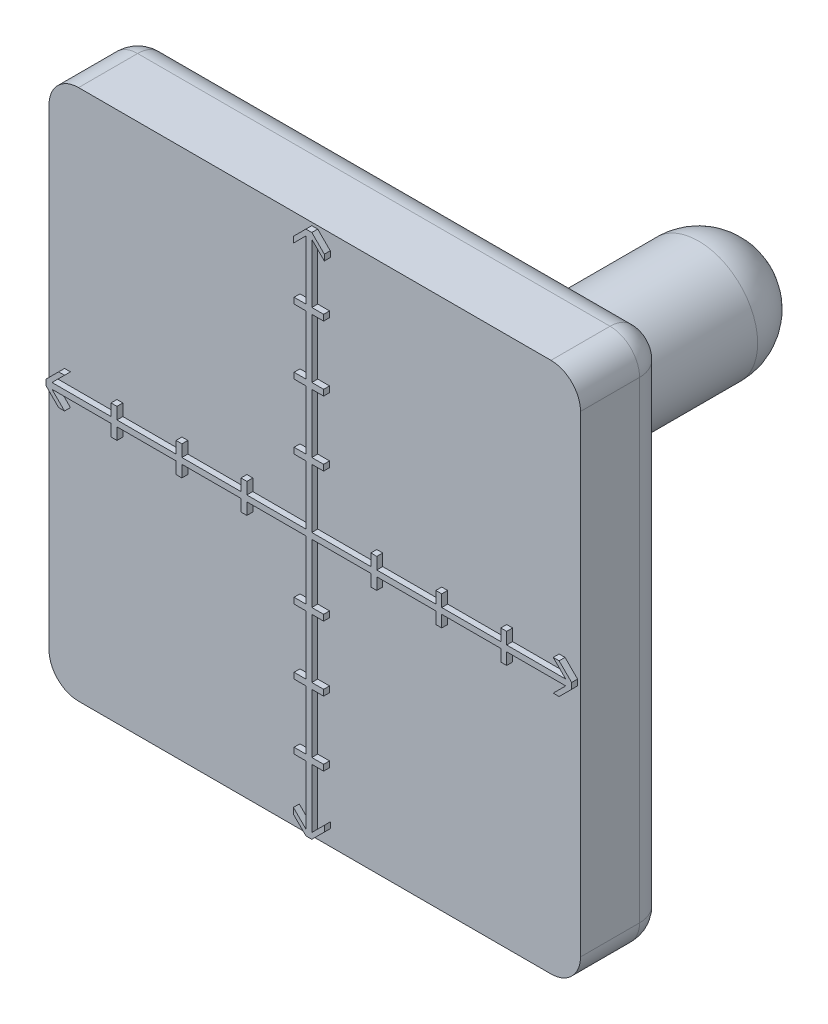
SolidWorks part; units mm, degrees
ref_plane "Alzado" through (0, 0, 0) normal (0, 0, 1) x (1, 0, 0)
ref_plane "Planta" through (0, 0, 0) normal (0, 1, 0) x (1, 0, 0)
ref_plane "Vista lateral" through (0, 0, 0) normal (1, 0, 0) x (0, 0, -1)
sketch "Croquis1" plane through (0, 0, 0) normal (0, 0, 1) x (1, 0, 0)
  line L1 (-45, -45) -> (45, -45)
  line L2 (-45, -45) -> (-45, 45)
  line L3 (-45, 45) -> (45, 45)
  line L4 (45, -45) -> (45, 45)
  line L5 (-45, -45) -> (45, 45) construction
  line L6 (-45, 45) -> (45, -45) construction
  point P0 (0, 0)
  dimension "D1" = 90
  dimension "D2" = 90
extrude "Saliente-Extruir2" add sketch "Croquis1" along normal blind 15
sketch "Croquis2" plane through (0, 0, 0) normal (0, 0, -1) x (-1, 0, 0)
  circle A0 centre (0, 0) radius 10
extrude "Saliente-Extruir3" add sketch "Croquis2" along normal blind 60
sketch "Croquis3" plane through (0, 0, 15) normal (0, 0, 1) x (1, 0, 0)
  line L14 (10.5, 0.5) -> (10.5, 2.5)
  line L15 (10.5, 2.5) -> (11.5, 2.5)
  line L16 (11.5, 2.5) -> (11.5, 0.5)
  line L18 (21.5, 0.5) -> (21.5, 2.5)
  line L19 (21.5, 2.5) -> (22.5, 2.5)
  line L20 (22.5, 2.5) -> (22.5, 0.5)
  line L22 (32.5, 0.5) -> (32.5, 2.5)
  line L23 (32.5, 2.5) -> (33.5, 2.5)
  line L24 (33.5, 2.5) -> (33.5, 0.5)
  line L25 (43.5, 0.5) -> (41.3787, 2.6213)
  line L26 (41.3787, 2.6213) -> (42.3787, 2.6213)
  line L27 (42.3787, 2.6213) -> (44.5, 0.5)
  line L28 (0, -41.25) -> (0, 41.25) construction
  line L29 (-42.3787, 2.6213) -> (-44.5, 0.5)
  line L30 (-41.3787, 2.6213) -> (-42.3787, 2.6213)
  line L31 (-43.5, 0.5) -> (-41.3787, 2.6213)
  line L32 (-33.5, 2.5) -> (-33.5, 0.5)
  line L33 (-32.5, 2.5) -> (-33.5, 2.5)
  line L34 (-32.5, 0.5) -> (-32.5, 2.5)
  line L35 (-22.5, 2.5) -> (-22.5, 0.5)
  line L36 (-21.5, 2.5) -> (-22.5, 2.5)
  line L37 (-21.5, 0.5) -> (-21.5, 2.5)
  line L38 (-11.5, 2.5) -> (-11.5, 0.5)
  line L39 (-10.5, 2.5) -> (-11.5, 2.5)
  line L40 (-10.5, 0.5) -> (-10.5, 2.5)
  line L45 (41.25, 0) -> (-41.25, 0) construction
  line L46 (42.3787, -2.6213) -> (44.5, -0.5)
  line L47 (41.3787, -2.6213) -> (42.3787, -2.6213)
  line L48 (43.5, -0.5) -> (41.3787, -2.6213)
  line L49 (33.5, -2.5) -> (33.5, -0.5)
  line L50 (32.5, -2.5) -> (33.5, -2.5)
  line L51 (32.5, -0.5) -> (32.5, -2.5)
  line L52 (22.5, -2.5) -> (22.5, -0.5)
  line L53 (21.5, -2.5) -> (22.5, -2.5)
  line L54 (21.5, -0.5) -> (21.5, -2.5)
  line L55 (11.5, -2.5) -> (11.5, -0.5)
  line L56 (10.5, -2.5) -> (11.5, -2.5)
  line L57 (10.5, -0.5) -> (10.5, -2.5)
  line L62 (-10.5, -0.5) -> (-10.5, -2.5)
  line L63 (-10.5, -2.5) -> (-11.5, -2.5)
  line L64 (-11.5, -2.5) -> (-11.5, -0.5)
  line L65 (-21.5, -0.5) -> (-21.5, -2.5)
  line L66 (-21.5, -2.5) -> (-22.5, -2.5)
  line L67 (-22.5, -2.5) -> (-22.5, -0.5)
  line L68 (-32.5, -0.5) -> (-32.5, -2.5)
  line L69 (-32.5, -2.5) -> (-33.5, -2.5)
  line L70 (-33.5, -2.5) -> (-33.5, -0.5)
  line L71 (-43.5, -0.5) -> (-41.3787, -2.6213)
  line L72 (-41.3787, -2.6213) -> (-42.3787, -2.6213)
  line L73 (-42.3787, -2.6213) -> (-44.5, -0.5)
  line L78 (-33.5, 0.5) -> (-43.5, 0.5)
  line L80 (-0.5, 10.5) -> (-2.5, 10.5)
  line L81 (-2.5, 10.5) -> (-2.5, 11.5)
  line L82 (-2.5, 11.5) -> (-0.5, 11.5)
  line L83 (-0.5, 21.5) -> (-2.5, 21.5)
  line L84 (-2.5, 21.5) -> (-2.5, 22.5)
  line L85 (-2.5, 22.5) -> (-0.5, 22.5)
  line L86 (-0.5, 32.5) -> (-2.5, 32.5)
  line L87 (-2.5, 32.5) -> (-2.5, 33.5)
  line L88 (-2.5, 33.5) -> (-0.5, 33.5)
  line L89 (-0.5, 43.5) -> (-2.6213, 41.3787)
  line L90 (-2.6213, 41.3787) -> (-2.6213, 42.3787)
  line L91 (-2.6213, 42.3787) -> (-0.5, 44.5)
  line L92 (-2.6213, -42.3787) -> (-0.5, -44.5)
  line L93 (-2.6213, -41.3787) -> (-2.6213, -42.3787)
  line L94 (-0.5, -43.5) -> (-2.6213, -41.3787)
  line L95 (-2.5, -33.5) -> (-0.5, -33.5)
  line L96 (-2.5, -32.5) -> (-2.5, -33.5)
  line L97 (-0.5, -32.5) -> (-2.5, -32.5)
  line L98 (-2.5, -22.5) -> (-0.5, -22.5)
  line L99 (-2.5, -21.5) -> (-2.5, -22.5)
  line L100 (-0.5, -21.5) -> (-2.5, -21.5)
  line L101 (-2.5, -11.5) -> (-0.5, -11.5)
  line L102 (-2.5, -10.5) -> (-2.5, -11.5)
  line L103 (-0.5, -10.5) -> (-2.5, -10.5)
  line L108 (2.6213, 42.3787) -> (0.5, 44.5)
  line L109 (2.6213, 41.3787) -> (2.6213, 42.3787)
  line L110 (0.5, 43.5) -> (2.6213, 41.3787)
  line L111 (2.5, 33.5) -> (0.5, 33.5)
  line L112 (2.5, 32.5) -> (2.5, 33.5)
  line L113 (0.5, 32.5) -> (2.5, 32.5)
  line L114 (2.5, 22.5) -> (0.5, 22.5)
  line L115 (2.5, 21.5) -> (2.5, 22.5)
  line L116 (0.5, 21.5) -> (2.5, 21.5)
  line L117 (2.5, 11.5) -> (0.5, 11.5)
  line L118 (2.5, 10.5) -> (2.5, 11.5)
  line L119 (0.5, 10.5) -> (2.5, 10.5)
  line L124 (0.5, -10.5) -> (2.5, -10.5)
  line L125 (2.5, -10.5) -> (2.5, -11.5)
  line L126 (2.5, -11.5) -> (0.5, -11.5)
  line L127 (0.5, -21.5) -> (2.5, -21.5)
  line L128 (2.5, -21.5) -> (2.5, -22.5)
  line L129 (2.5, -22.5) -> (0.5, -22.5)
  line L130 (0.5, -32.5) -> (2.5, -32.5)
  line L131 (2.5, -32.5) -> (2.5, -33.5)
  line L132 (2.5, -33.5) -> (0.5, -33.5)
  line L133 (0.5, -43.5) -> (2.6213, -41.3787)
  line L134 (2.6213, -41.3787) -> (2.6213, -42.3787)
  line L135 (2.6213, -42.3787) -> (0.5, -44.5)
  line L136 (-0.5, -32.5) -> (-0.5, -22.5)
  line L138 (0.5, 43.5) -> (0.5, 33.5)
  line L139 (-0.5, 44.5) -> (0.5, 44.5)
  line L140 (-0.5, -43.5) -> (-0.5, -33.5)
  line L141 (0.5, -33.5) -> (0.5, -43.5)
  line L142 (-0.5, -21.5) -> (-0.5, -11.5)
  line L143 (0.5, -22.5) -> (0.5, -32.5)
  line L144 (0.5, -11.5) -> (0.5, -21.5)
  line L145 (-0.5, -10.5) -> (-0.5, -0.5)
  line L146 (0.5, 10.5) -> (0.5, 0.5)
  line L147 (-0.5, 11.5) -> (-0.5, 21.5)
  line L148 (0.5, 21.5) -> (0.5, 11.5)
  line L149 (-0.5, 22.5) -> (-0.5, 32.5)
  line L150 (-0.5, 33.5) -> (-0.5, 43.5)
  line L151 (0.5, 32.5) -> (0.5, 22.5)
  line L152 (-44.5, 0.5) -> (-44.5, -0.5)
  line L153 (-33.5, -0.5) -> (-43.5, -0.5)
  line L154 (-22.5, 0.5) -> (-32.5, 0.5)
  line L155 (-22.5, -0.5) -> (-32.5, -0.5)
  line L156 (-11.5, 0.5) -> (-21.5, 0.5)
  line L157 (-11.5, -0.5) -> (-21.5, -0.5)
  line L158 (-0.5, -0.5) -> (-10.5, -0.5)
  line L159 (-0.5, 0.5) -> (-0.5, 10.5)
  line L160 (-0.5, -0.5) -> (-0.5, -10.5)
  line L161 (0.5, -0.5) -> (0.5, -10.5)
  line L162 (0.5, -0.5) -> (0.5, -10.5)
  line L163 (-0.5, 0.5) -> (-10.5, 0.5)
  line L164 (10.5, 0.5) -> (0.5, 0.5)
  line L165 (10.5, -0.5) -> (0.5, -0.5)
  line L166 (21.5, 0.5) -> (11.5, 0.5)
  line L167 (21.5, -0.5) -> (11.5, -0.5)
  line L168 (32.5, -0.5) -> (22.5, -0.5)
  line L169 (32.5, 0.5) -> (22.5, 0.5)
  line L170 (43.5, 0.5) -> (33.5, 0.5)
  line L171 (43.5, -0.5) -> (33.5, -0.5)
  line L172 (-0.5, 10.5) -> (-0.5, 0.5)
  line L173 (0.5, 10.5) -> (0.5, 0.5)
  line L174 (-0.5, 21.5) -> (-0.5, 11.5)
  line L175 (0.5, 21.5) -> (0.5, 11.5)
  line L176 (0.5, 32.5) -> (0.5, 22.5)
  line L177 (-0.5, 32.5) -> (-0.5, 22.5)
  line L178 (-0.5, 43.5) -> (-0.5, 33.5)
  line L179 (0.5, 43.5) -> (0.5, 33.5)
  line L182 (-0.5, -33.5) -> (-0.5, -43.5)
  line L183 (0.5, -33.5) -> (0.5, -43.5)
  line L184 (-0.5, -22.5) -> (-0.5, -32.5)
  line L185 (0.5, -22.5) -> (0.5, -32.5)
  line L186 (0.5, -11.5) -> (0.5, -21.5)
  line L187 (-0.5, -11.5) -> (-0.5, -21.5)
  line L188 (44.5, 0.5) -> (44.5, -0.5)
  line L189 (-0.5, -44.5) -> (0.5, -44.5)
  dimension "D6" = 1
  dimension "D8" = 1
  dimension "D9" = 10
  dimension "D10" = 1
  dimension "D12" = 10
  dimension "D13" = 1
  dimension "D14" = 1
  dimension "D16" = 10
extrude "Saliente-Extruir4" add sketch "Croquis3" along normal blind 1 contours L92 L189 L135 L134 L133 L141 L132 L131 L130 L143 L129 L128 L127 L144 L126 L125 L124 L161 L165 L57 L56 L55 L167 L54 L53 L52 L168 L51 L50 L49 L171 L48 L47 L46 L188 L27 L26 L25 L170 L24 L23 L22 L169 L20 L19 L18 L166 L16 L15 L14 L164
fillet "Redondeo1" radius 5 4 edges at (-45, -45, 7.5) (45, -45, 7.5) (-45, 45, 7.5) (45, 45, 7.5)
fillet "Redondeo2" radius 5 8 edges at (-43.5355, 43.5355, 0) (0, 45, 0) (43.5355, 43.5355, 0) (45, 0, 0) (43.5355, -43.5355, 0) (0, -45, 0) (-43.5355, -43.5355, 0) (-45, 0, 0)
fillet "Redondeo3" radius 5 1 edges at (-10, 0, 0)
fillet "Redondeo4" radius 10 1 edges at (-10, 0, -60)
